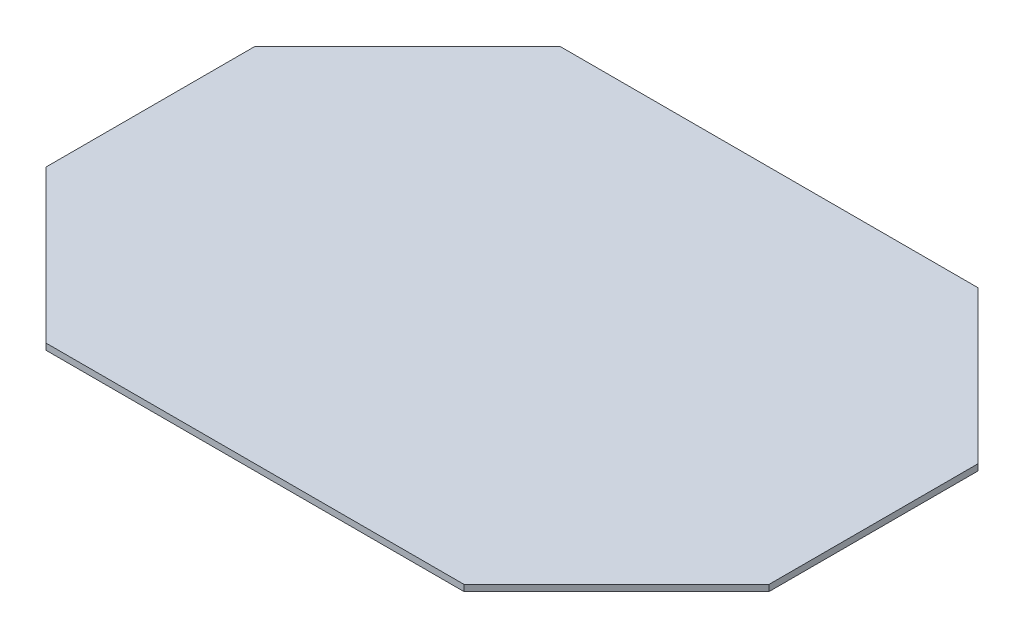
SolidWorks part; units mm, degrees
ref_plane "Plan de face" through (0, 0, 0) normal (0, 0, 1) x (1, 0, 0)
ref_plane "Plan de dessus" through (0, 0, 0) normal (0, 1, 0) x (1, 0, 0)
ref_plane "Plan de droite" through (0, 0, 0) normal (1, 0, 0) x (0, 0, -1)
sketch "Esquisse1" plane through (0, 0, 0) normal (0, 1, 0) x (1, 0, 0)
  line L0 (0, 0) -> (0, 100)
  line L1 (0, 100) -> (72.9167, 172.9167)
  line L2 (72.9167, 172.9167) -> (272.9167, 172.9167)
  line L3 (272.9167, 172.9167) -> (345.8333, 100)
  line L4 (345.8333, 100) -> (345.8333, 0)
  line L5 (345.8333, 0) -> (272.9167, -72.9167)
  line L6 (272.9167, -72.9167) -> (72.9167, -72.9167)
  line L7 (72.9167, -72.9167) -> (0, 0)
  line L8 (0, 50) -> (345.8333, 50) construction
  line L9 (172.9167, 172.9167) -> (172.9167, -72.9167) construction
  dimension "D1" = 100
  dimension "D2" = 200
extrude "Extrusion1" add sketch "Esquisse1" along normal blind 3
